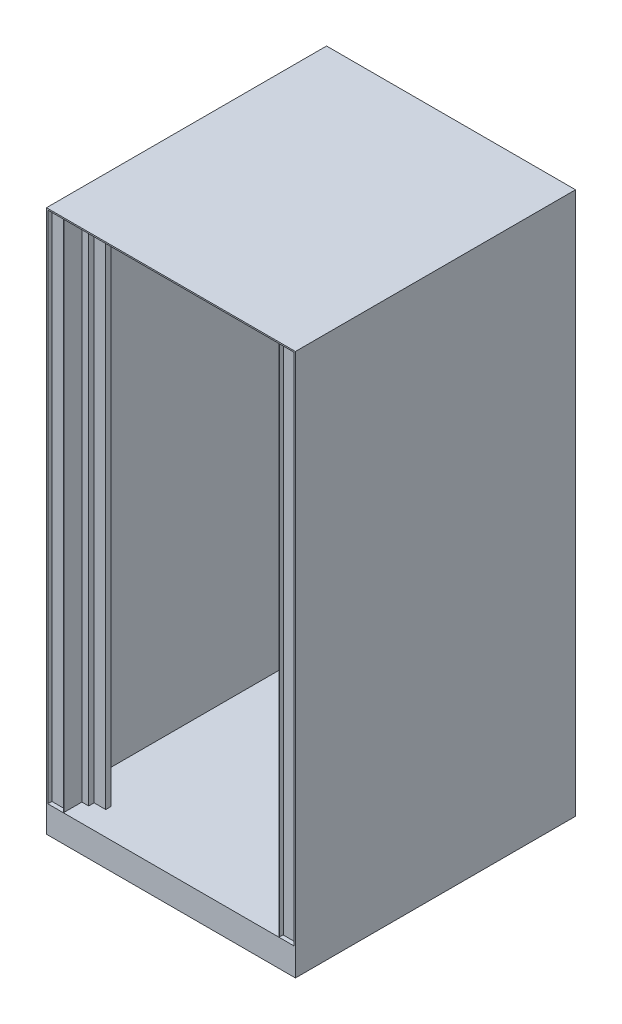
SolidWorks part; units mm, degrees
ref_plane "Alzado" through (0, 0, 0) normal (0, 0, 1) x (1, 0, 0)
ref_plane "Planta" through (0, 0, 0) normal (0, 1, 0) x (1, 0, 0)
ref_plane "Vista lateral" through (0, 0, 0) normal (1, 0, 0) x (0, 0, -1)
sketch "Croquis1" plane through (0, 0, 0) normal (0, 0, 1) x (1, 0, 0)
  line L1 (-460, -1002.5) -> (460, -1002.5)
  line L2 (-460, -1002.5) -> (-460, 1002.5)
  line L3 (-460, 1002.5) -> (460, 1002.5)
  line L4 (460, -1002.5) -> (460, 1002.5)
  line L5 (-460, -1002.5) -> (460, 1002.5) construction
  line L6 (-460, 1002.5) -> (460, -1002.5) construction
  point P0 (0, 0)
  dimension "D1" = 2005
  dimension "D2" = 920
extrude "Saliente-Extruir1" add sketch "Croquis1" along normal blind 1035
sketch "Croquis2" plane through (0, 0, 1035) normal (0, 0, 1) x (1, 0, 0)
  line L0 (460, -1002.5) -> (460, 1002.5) construction
  line L1 (-455, -902.5) -> (455, -902.5)
  line L2 (-455, -902.5) -> (-455, 997.5)
  line L3 (-455, 997.5) -> (455, 997.5)
  line L4 (455, -902.5) -> (455, 997.5)
  line L5 (-455, -902.5) -> (455, 997.5) construction
  line L6 (-455, 997.5) -> (455, -902.5) construction
  line L7 (-460, 1002.5) -> (-460, -1002.5) construction
  line L8 (-460, -1002.5) -> (460, -1002.5) construction
  line L9 (460, 1002.5) -> (-460, 1002.5) construction
  point P0 (0, 47.5)
  dimension "D1" = 5
  dimension "D2" = 5
  dimension "D3" = 100
  dimension "D4" = 5
extrude "Cortar-Extruir1" cut sketch "Croquis2" against normal blind 1025
sketch "Croquis3" plane through (0, -902.5, 0) normal (0, 1, 0) x (1, 0, 0)
  line L0 (-406, -59) -> (-425, -59)
  line L1 (455, -10) -> (-455, -10) construction
  line L2 (400, -10) -> (400, -40)
  line L3 (425, -65) -> (425, -59)
  line L4 (425, -65) -> (455, -65)
  line L5 (455, -10) -> (455, -1035) construction
  line L6 (400, -40) -> (406, -40)
  line L7 (406, -40) -> (406, -59)
  line L8 (406, -59) -> (425, -59)
  line L9 (0, -10) -> (0, -588.3367) construction
  line L10 (-406, -40) -> (-406, -59)
  line L11 (-400, -40) -> (-406, -40)
  line L12 (-425, -65) -> (-455, -65)
  line L13 (-425, -65) -> (-425, -59)
  line L14 (-400, -10) -> (-400, -40)
  line L15 (-455, -65) -> (-455, -10)
  line L16 (-455, -10) -> (-400, -10)
  line L17 (400, -10) -> (455, -10)
  line L18 (455, -10) -> (455, -65)
  dimension "D3" = 6
  dimension "D4" = 30
  dimension "D5" = 6
  dimension "D6" = 30
extrude "Saliente-Extruir2" add sketch "Croquis3" along normal up to surface (1900 mm away) up to face at (0, 997.5, 522.5)
sketch "Croquis4" plane through (0, -902.5, 0) normal (0, 1, 0) x (1, 0, 0)
  line L0 (-455, -965) -> (-425, -965)
  line L1 (-455, -65) -> (-455, -1035) construction
  line L2 (-455, -65) -> (-425, -65) construction
  line L3 (-400, -989.9132) -> (-400, -1019.9132)
  line L4 (-400, -1019.9132) -> (-455, -1019.9132)
  line L5 (-425, -965) -> (-425, -971)
  line L6 (-400, -989.9132) -> (-406, -989.9132)
  line L7 (-425, -971) -> (-406, -971)
  line L8 (-406, -971) -> (-406, -989.9132)
  line L9 (0, -1035) -> (0, -858.0791) construction
  line L10 (460, -1035) -> (-460, -1035) construction
  line L11 (-455, -1019.9132) -> (-455, -965)
  line L12 (406, -971) -> (406, -989.9132)
  line L13 (425, -971) -> (406, -971)
  line L14 (400, -989.9132) -> (406, -989.9132)
  line L15 (425, -965) -> (425, -971)
  line L16 (400, -1019.9132) -> (455, -1019.9132)
  line L17 (400, -989.9132) -> (400, -1019.9132)
  line L18 (455, -965) -> (425, -965)
  line L19 (455, -1019.9132) -> (455, -965)
  point P6 (-440, -65)
  point P7 (-440, -965)
  dimension "D1" = 900
  dimension "D4" = 30
  dimension "D5" = 6
  dimension "D6" = 30
  dimension "D7" = 6
extrude "Saliente-Extruir3" add sketch "Croquis4" along normal up to surface (1900 mm away) up to face at (0, 997.5, 171.625)
sketch "Croquis5" plane through (0, -902.5, 0) normal (0, 1, 0) x (1, 0, 0)
  line L0 (-399, -1033) -> (-399, -965)
  line L1 (-455, -65) -> (-455, -965) construction
  line L2 (-399, -965) -> (-374, -965)
  line L3 (-374, -965) -> (-374, -945)
  line L4 (-374, -945) -> (-331, -945)
  line L5 (-331, -945) -> (-331, -927)
  line L6 (-331, -927) -> (-329.5, -927)
  line L7 (-329.5, -927) -> (-329.5, -946.5)
  line L8 (-329.5, -946.5) -> (-372.5, -946.5)
  line L9 (-372.5, -946.5) -> (-372.5, -966.5)
  line L10 (-372.5, -966.5) -> (-397.5, -966.5)
  line L11 (-397.5, -966.5) -> (-397.5, -981.8548)
  line L12 (-397.5, -981.8548) -> (-397.5, -1033)
  line L13 (-397.5, -1033) -> (-399, -1033)
  line L14 (0, -1035) -> (0, -826.8865) construction
  line L15 (460, -1035) -> (-460, -1035) construction
  line L16 (397.5, -1033) -> (399, -1033)
  line L17 (397.5, -981.8548) -> (397.5, -1033)
  line L18 (397.5, -966.5) -> (397.5, -981.8548)
  line L19 (372.5, -966.5) -> (397.5, -966.5)
  line L20 (372.5, -946.5) -> (372.5, -966.5)
  line L21 (329.5, -946.5) -> (372.5, -946.5)
  line L22 (329.5, -927) -> (329.5, -946.5)
  line L23 (331, -927) -> (329.5, -927)
  line L24 (331, -945) -> (331, -927)
  line L25 (374, -945) -> (331, -945)
  line L26 (374, -965) -> (374, -945)
  line L27 (399, -965) -> (374, -965)
  line L28 (399, -1033) -> (399, -965)
  dimension "D1" = 56
  dimension "D2" = 0
  dimension "D3" = 68
  dimension "D4" = 25
  dimension "D5" = 20
  dimension "D6" = 43
  dimension "D7" = 18
  dimension "D8" = 1.5
  dimension "D9" = 1.5
  dimension "D10" = 1.5
  dimension "D11" = 1.5
  dimension "D12" = 1.5
extrude "Saliente-Extruir4" add sketch "Croquis5" along normal up to surface (1900 mm away) up to face at (0, 997.5, 579.0408)
